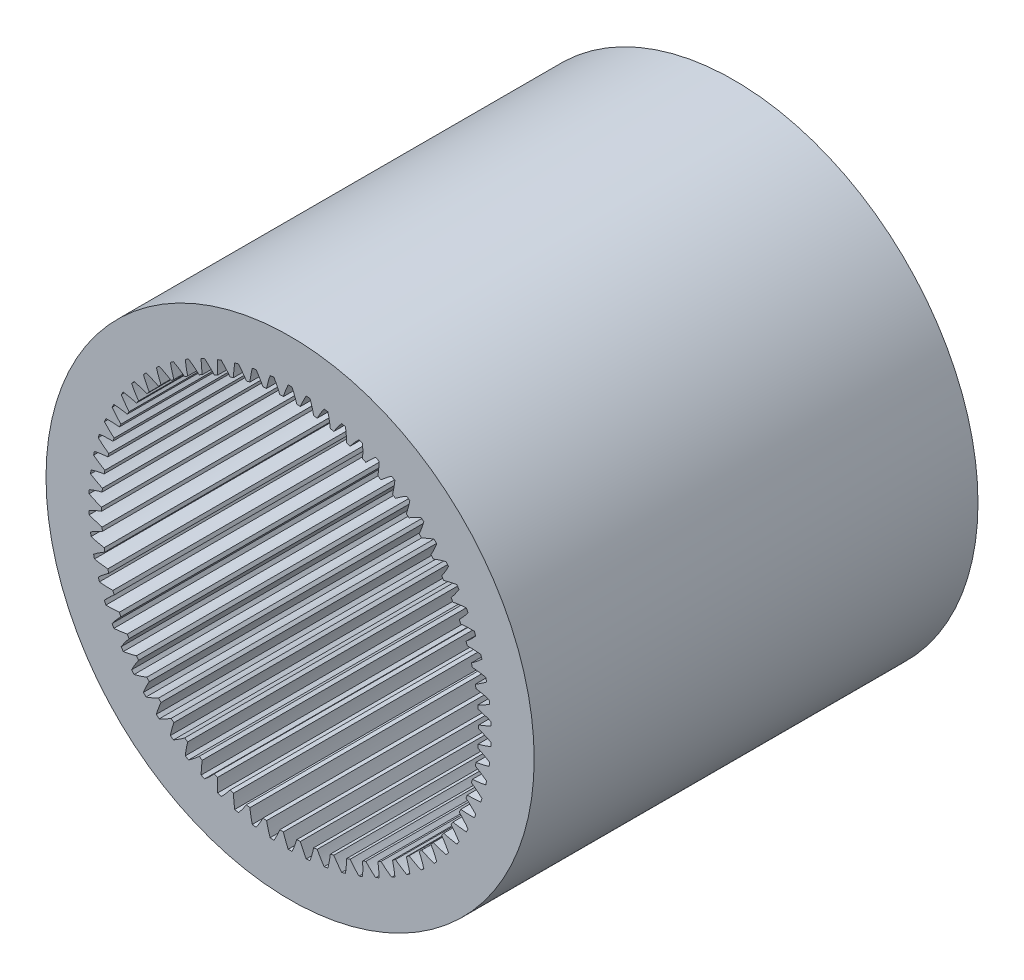
SolidWorks part; units mm, degrees
ref_plane "Front Plane" through (0, 0, 0) normal (0, 0, 1) x (1, 0, 0)
ref_plane "Top Plane" through (0, 0, 0) normal (0, 1, 0) x (1, 0, 0)
ref_plane "Right Plane" through (0, 0, 0) normal (1, 0, 0) x (0, 0, -1)
sketch "Sketch1" plane through (0, 0, 0) normal (0, 0, 1) x (1, 0, 0)
  circle A2 centre (0, 0) radius 11
  arc A4 (-8.3487, -1.5969) -> (-8.8549, -1.9333) centre (-6.1864, -5.4002) ccw
  arc A8 (-8.3774, -1.4384) -> (-8.3487, -1.5969) centre (0, 0) ccw
  arc A9 (-8.8549, -1.9333) -> (-8.8168, -2.1002) centre (0, 0) ccw
  arc A10 (-8.8168, -2.1002) -> (-8.2147, -2.1836) centre (-7.9168, 2.1812) ccw
  arc A11 (-8.4726, -0.6817) -> (-8.4582, -0.8421) centre (0, 0) ccw
  arc A12 (-8.4582, -0.8421) -> (-8.9926, -1.1317) centre (-6.6455, -4.8239) ccw
  arc A13 (-8.9926, -1.1317) -> (-8.9696, -1.3014) centre (0, 0) ccw
  arc A14 (-8.9696, -1.3014) -> (-8.3774, -1.4384) centre (-7.6894, 2.8821) ccw
  arc A15 (-8.4996, 0.0805) -> (-8.4996, -0.0805) centre (0, 0) ccw
  arc A16 (-8.4996, -0.0805) -> (-9.0578, -0.3211) centre (-7.0512, -4.2088) ccw
  arc A17 (-9.0578, -0.3211) -> (-9.0501, -0.4921) centre (0, 0) ccw
  arc A18 (-9.0501, -0.4921) -> (-8.4726, -0.6817) centre (-7.4001, 3.5598) ccw
  arc A19 (-8.4582, 0.8421) -> (-8.4726, 0.6817) centre (0, 0) ccw
  arc A20 (-8.4726, 0.6817) -> (-9.0501, 0.4921) centre (-7.4001, -3.5598) ccw
  arc A21 (-9.0501, 0.4921) -> (-9.0578, 0.3211) centre (0, 0) ccw
  arc A22 (-9.0578, 0.3211) -> (-8.4996, 0.0805) centre (-7.0512, 4.2088) ccw
  arc A23 (-8.3487, 1.5969) -> (-8.3774, 1.4384) centre (0, 0) ccw
  arc A24 (-8.3774, 1.4384) -> (-8.9696, 1.3014) centre (-7.6894, -2.8821) ccw
  arc A25 (-8.9696, 1.3014) -> (-8.9926, 1.1317) centre (0, 0) ccw
  arc A26 (-8.9926, 1.1317) -> (-8.4582, 0.8421) centre (-6.6455, 4.8239) ccw
  arc A27 (-8.1719, 2.3388) -> (-8.2147, 2.1836) centre (0, 0) ccw
  arc A28 (-8.2147, 2.1836) -> (-8.8168, 2.1002) centre (-7.9168, -2.1812) ccw
  arc A29 (-8.8168, 2.1002) -> (-8.8549, 1.9333) centre (0, 0) ccw
  arc A30 (-8.8549, 1.9333) -> (-8.3487, 1.5969) centre (-6.1864, 5.4002) ccw
  arc A31 (-7.9294, 3.0619) -> (-7.9859, 2.9112) centre (0, 0) ccw
  arc A32 (-7.9859, 2.9112) -> (-8.5931, 2.8821) centre (-8.0804, -1.4628) ccw
  arc A33 (-8.5931, 2.8821) -> (-8.646, 2.7192) centre (0, 0) ccw
  arc A34 (-8.646, 2.7192) -> (-8.1719, 2.3388) centre (-5.6774, 5.933) ccw
  arc A35 (-7.623, 3.7604) -> (-7.6928, 3.6153) centre (0, 0) ccw
  arc A36 (-7.6928, 3.6153) -> (-8.3001, 3.6407) centre (-8.179, -0.7326) ccw
  arc A37 (-8.3001, 3.6407) -> (-8.3674, 3.4833) centre (0, 0) ccw
  arc A38 (-8.3674, 3.4833) -> (-7.9294, 3.0619) centre (-5.1227, 6.418) ccw
  arc A39 (-7.2552, 4.4286) -> (-7.3378, 4.2903) centre (0, 0) ccw
  arc A40 (-7.3378, 4.2903) -> (-7.9404, 4.3701) centre (-8.2118, 0.0035) ccw
  arc A41 (-7.9404, 4.3701) -> (-8.0215, 4.2193) centre (0, 0) ccw
  arc A42 (-8.0215, 4.2193) -> (-7.623, 3.7604) centre (-4.5268, 6.8514) ccw
  arc A43 (-6.829, 5.0611) -> (-6.9237, 4.9308) centre (0, 0) ccw
  arc A44 (-6.9237, 4.9308) -> (-7.5167, 5.0643) centre (-8.1784, 0.7396) ccw
  arc A45 (-7.5167, 5.0643) -> (-7.611, 4.9214) centre (0, 0) ccw
  arc A46 (-7.611, 4.9214) -> (-7.2552, 4.4286) centre (-3.8944, 7.2296) ccw
  arc A47 (-6.3478, 5.6529) -> (-6.4538, 5.5316) centre (0, 0) ccw
  arc A48 (-6.4538, 5.5316) -> (-7.0324, 5.7177) centre (-8.0792, 1.4697) ccw
  arc A49 (-7.0324, 5.7177) -> (-7.1392, 5.5838) centre (0, 0) ccw
  arc A50 (-7.1392, 5.5838) -> (-6.829, 5.0611) centre (-3.2307, 7.5496) ccw
  arc A51 (-5.8156, 6.1991) -> (-5.932, 6.0878) centre (0, 0) ccw
  arc A52 (-5.932, 6.0878) -> (-6.4916, 6.325) centre (-7.9149, 2.188) ccw
  arc A53 (-6.4916, 6.325) -> (-6.6099, 6.2013) centre (0, 0) ccw
  arc A54 (-6.6099, 6.2013) -> (-6.3478, 5.6529) centre (-2.5409, 7.8088) ccw
  arc A55 (-5.2365, 6.6955) -> (-5.3624, 6.5951) centre (0, 0) ccw
  arc A56 (-5.3624, 6.5951) -> (-5.8985, 6.8815) centre (-7.6869, 2.8887) ccw
  arc A57 (-5.8985, 6.8815) -> (-6.0274, 6.7688) centre (0, 0) ccw
  arc A58 (-6.0274, 6.7688) -> (-5.8156, 6.1991) centre (-1.8307, 8.0051) ccw
  arc A59 (-4.6152, 7.1379) -> (-4.7496, 7.0492) centre (0, 0) ccw
  arc A60 (-4.7496, 7.0492) -> (-5.2579, 7.3825) centre (-7.397, 3.5661) ccw
  arc A61 (-5.2579, 7.3825) -> (-5.3964, 7.2819) centre (0, 0) ccw
  arc A62 (-5.3964, 7.2819) -> (-5.2365, 6.6955) centre (-1.1058, 8.137) ccw
  arc A63 (-3.9568, 7.5229) -> (-4.0986, 7.4466) centre (0, 0) ccw
  arc A64 (-4.0986, 7.4466) -> (-4.575, 7.8241) centre (-7.0476, 4.2148) ccw
  arc A65 (-4.575, 7.8241) -> (-4.7219, 7.7363) centre (0, 0) ccw
  arc A66 (-4.7219, 7.7363) -> (-4.6152, 7.1379) centre (-0.3719, 8.2033) ccw
  arc A67 (-3.2665, 7.8473) -> (-3.4146, 7.784) centre (0, 0) ccw
  arc A68 (-3.4146, 7.784) -> (-3.8552, 8.2027) centre (-6.6414, 4.8296) ccw
  arc A69 (-3.8552, 8.2027) -> (-4.0095, 8.1284) centre (0, 0) ccw
  arc A70 (-4.0095, 8.1284) -> (-3.9568, 7.5229) centre (0.3649, 8.2037) ccw
  arc A71 (-2.55, 8.1085) -> (-2.7031, 8.0587) centre (0, 0) ccw
  arc A72 (-2.7031, 8.0587) -> (-3.1044, 8.5153) centre (-6.1817, 5.4055) ccw
  arc A73 (-3.1044, 8.5153) -> (-3.2647, 8.4551) centre (0, 0) ccw
  arc A74 (-3.2647, 8.4551) -> (-3.2665, 7.8473) centre (1.0988, 8.1379) ccw
  arc A75 (-1.8129, 8.3044) -> (-1.9698, 8.2686) centre (0, 0) ccw
  arc A76 (-1.9698, 8.2686) -> (-2.3286, 8.7593) centre (-5.6723, 5.9379) ccw
  arc A77 (-2.3286, 8.7593) -> (-2.4936, 8.7137) centre (0, 0) ccw
  arc A78 (-2.4936, 8.7137) -> (-2.55, 8.1085) centre (1.8239, 8.0067) ccw
  arc A79 (-1.0611, 8.4335) -> (-1.2207, 8.4119) centre (0, 0) ccw
  arc A80 (-1.2207, 8.4119) -> (-1.5341, 8.9327) centre (-5.1172, 6.4224) ccw
  arc A81 (-1.5341, 8.9327) -> (-1.7025, 8.9022) centre (0, 0) ccw
  arc A82 (-1.7025, 8.9022) -> (-1.8129, 8.3044) centre (2.5342, 7.8109) ccw
  arc A83 (-0.3009, 8.4947) -> (-0.4618, 8.4874) centre (0, 0) ccw
  arc A84 (-0.4618, 8.4874) -> (-0.7272, 9.0343) centre (-4.5209, 6.8553) ccw
  arc A85 (-0.7272, 9.0343) -> (-0.8977, 9.0189) centre (0, 0) ccw
  arc A86 (-0.8977, 9.0189) -> (-1.0611, 8.4335) centre (3.2242, 7.5523) ccw
  arc A87 (0.4618, 8.4874) -> (0.3009, 8.4947) centre (0, 0) ccw
  arc A88 (0.3009, 8.4947) -> (0.0856, 9.0631) centre (-3.8882, 7.2329) ccw
  arc A89 (0.0856, 9.0631) -> (-0.0856, 9.0631) centre (0, 0) ccw
  arc A90 (-0.0856, 9.0631) -> (-0.3009, 8.4947) centre (3.8882, 7.2329) ccw
  arc A91 (1.2207, 8.4119) -> (1.0611, 8.4335) centre (0, 0) ccw
  arc A92 (1.0611, 8.4335) -> (0.8977, 9.0189) centre (-3.2242, 7.5523) ccw
  arc A93 (0.8977, 9.0189) -> (0.7272, 9.0343) centre (0, 0) ccw
  arc A94 (0.7272, 9.0343) -> (0.4618, 8.4874) centre (4.5209, 6.8553) ccw
  arc A95 (1.9698, 8.2686) -> (1.8129, 8.3044) centre (0, 0) ccw
  arc A96 (1.8129, 8.3044) -> (1.7025, 8.9022) centre (-2.5342, 7.8109) ccw
  arc A97 (1.7025, 8.9022) -> (1.5341, 8.9327) centre (0, 0) ccw
  arc A98 (1.5341, 8.9327) -> (1.2207, 8.4119) centre (5.1172, 6.4224) ccw
  arc A99 (2.7031, 8.0587) -> (2.55, 8.1085) centre (0, 0) ccw
  arc A100 (2.55, 8.1085) -> (2.4936, 8.7137) centre (-1.8239, 8.0067) ccw
  arc A101 (2.4936, 8.7137) -> (2.3286, 8.7593) centre (0, 0) ccw
  arc A102 (2.3286, 8.7593) -> (1.9698, 8.2686) centre (5.6723, 5.9379) ccw
  arc A103 (3.4146, 7.784) -> (3.2665, 7.8473) centre (0, 0) ccw
  arc A104 (3.2665, 7.8473) -> (3.2647, 8.4551) centre (-1.0988, 8.1379) ccw
  arc A105 (3.2647, 8.4551) -> (3.1044, 8.5153) centre (0, 0) ccw
  arc A106 (3.1044, 8.5153) -> (2.7031, 8.0587) centre (6.1817, 5.4055) ccw
  arc A107 (4.0986, 7.4466) -> (3.9568, 7.5229) centre (0, 0) ccw
  arc A108 (3.9568, 7.5229) -> (4.0095, 8.1284) centre (-0.3649, 8.2037) ccw
  arc A109 (4.0095, 8.1284) -> (3.8552, 8.2027) centre (0, 0) ccw
  arc A110 (3.8552, 8.2027) -> (3.4146, 7.784) centre (6.6414, 4.8296) ccw
  arc A111 (4.7496, 7.0492) -> (4.6152, 7.1379) centre (0, 0) ccw
  arc A112 (4.6152, 7.1379) -> (4.7219, 7.7363) centre (0.3719, 8.2033) ccw
  arc A113 (4.7219, 7.7363) -> (4.575, 7.8241) centre (0, 0) ccw
  arc A114 (4.575, 7.8241) -> (4.0986, 7.4466) centre (7.0476, 4.2148) ccw
  arc A115 (5.3624, 6.5951) -> (5.2365, 6.6955) centre (0, 0) ccw
  arc A116 (5.2365, 6.6955) -> (5.3964, 7.2819) centre (1.1058, 8.137) ccw
  arc A117 (5.3964, 7.2819) -> (5.2579, 7.3825) centre (0, 0) ccw
  arc A118 (5.2579, 7.3825) -> (4.7496, 7.0492) centre (7.397, 3.5661) ccw
  arc A119 (5.932, 6.0878) -> (5.8156, 6.1991) centre (0, 0) ccw
  arc A120 (5.8156, 6.1991) -> (6.0274, 6.7688) centre (1.8307, 8.0051) ccw
  arc A121 (6.0274, 6.7688) -> (5.8985, 6.8815) centre (0, 0) ccw
  arc A122 (5.8985, 6.8815) -> (5.3624, 6.5951) centre (7.6869, 2.8887) ccw
  arc A123 (6.4538, 5.5316) -> (6.3478, 5.6529) centre (0, 0) ccw
  arc A124 (6.3478, 5.6529) -> (6.6099, 6.2013) centre (2.5409, 7.8088) ccw
  arc A125 (6.6099, 6.2013) -> (6.4916, 6.325) centre (0, 0) ccw
  arc A126 (6.4916, 6.325) -> (5.932, 6.0878) centre (7.9149, 2.188) ccw
  arc A127 (6.9237, 4.9308) -> (6.829, 5.0611) centre (0, 0) ccw
  arc A128 (6.829, 5.0611) -> (7.1392, 5.5838) centre (3.2307, 7.5496) ccw
  arc A129 (7.1392, 5.5838) -> (7.0324, 5.7177) centre (0, 0) ccw
  arc A130 (7.0324, 5.7177) -> (6.4538, 5.5316) centre (8.0792, 1.4697) ccw
  arc A131 (7.3378, 4.2903) -> (7.2552, 4.4286) centre (0, 0) ccw
  arc A132 (7.2552, 4.4286) -> (7.611, 4.9214) centre (3.8944, 7.2296) ccw
  arc A133 (7.611, 4.9214) -> (7.5167, 5.0643) centre (0, 0) ccw
  arc A134 (7.5167, 5.0643) -> (6.9237, 4.9308) centre (8.1784, 0.7396) ccw
  arc A135 (7.6928, 3.6153) -> (7.623, 3.7604) centre (0, 0) ccw
  arc A136 (7.623, 3.7604) -> (8.0215, 4.2193) centre (4.5268, 6.8514) ccw
  arc A137 (8.0215, 4.2193) -> (7.9404, 4.3701) centre (0, 0) ccw
  arc A138 (7.9404, 4.3701) -> (7.3378, 4.2903) centre (8.2118, 0.0035) ccw
  arc A139 (7.9859, 2.9112) -> (7.9294, 3.0619) centre (0, 0) ccw
  arc A140 (7.9294, 3.0619) -> (8.3674, 3.4833) centre (5.1227, 6.418) ccw
  arc A141 (8.3674, 3.4833) -> (8.3001, 3.6407) centre (0, 0) ccw
  arc A142 (8.3001, 3.6407) -> (7.6928, 3.6153) centre (8.179, -0.7326) ccw
  arc A143 (8.2147, 2.1836) -> (8.1719, 2.3388) centre (0, 0) ccw
  arc A144 (8.1719, 2.3388) -> (8.646, 2.7192) centre (5.6774, 5.933) ccw
  arc A145 (8.646, 2.7192) -> (8.5931, 2.8821) centre (0, 0) ccw
  arc A146 (8.5931, 2.8821) -> (7.9859, 2.9112) centre (8.0804, -1.4628) ccw
  arc A147 (8.3774, 1.4384) -> (8.3487, 1.5969) centre (0, 0) ccw
  arc A148 (8.3487, 1.5969) -> (8.8549, 1.9333) centre (6.1864, 5.4002) ccw
  arc A149 (8.8549, 1.9333) -> (8.8168, 2.1002) centre (0, 0) ccw
  arc A150 (8.8168, 2.1002) -> (8.2147, 2.1836) centre (7.9168, -2.1812) ccw
  arc A151 (8.4726, 0.6817) -> (8.4582, 0.8421) centre (0, 0) ccw
  arc A152 (8.4582, 0.8421) -> (8.9926, 1.1317) centre (6.6455, 4.8239) ccw
  arc A153 (8.9926, 1.1317) -> (8.9696, 1.3014) centre (0, 0) ccw
  arc A154 (8.9696, 1.3014) -> (8.3774, 1.4384) centre (7.6894, -2.8821) ccw
  arc A155 (8.4996, -0.0805) -> (8.4996, 0.0805) centre (0, 0) ccw
  arc A156 (8.4996, 0.0805) -> (9.0578, 0.3211) centre (7.0512, 4.2088) ccw
  arc A157 (9.0578, 0.3211) -> (9.0501, 0.4921) centre (0, 0) ccw
  arc A158 (9.0501, 0.4921) -> (8.4726, 0.6817) centre (7.4001, -3.5598) ccw
  arc A159 (8.4582, -0.8421) -> (8.4726, -0.6817) centre (0, 0) ccw
  arc A160 (8.4726, -0.6817) -> (9.0501, -0.4921) centre (7.4001, 3.5598) ccw
  arc A161 (9.0501, -0.4921) -> (9.0578, -0.3211) centre (0, 0) ccw
  arc A162 (9.0578, -0.3211) -> (8.4996, -0.0805) centre (7.0512, -4.2088) ccw
  arc A163 (8.3487, -1.5969) -> (8.3774, -1.4384) centre (0, 0) ccw
  arc A164 (8.3774, -1.4384) -> (8.9696, -1.3014) centre (7.6894, 2.8821) ccw
  arc A165 (8.9696, -1.3014) -> (8.9926, -1.1317) centre (0, 0) ccw
  arc A166 (8.9926, -1.1317) -> (8.4582, -0.8421) centre (6.6455, -4.8239) ccw
  arc A167 (8.1719, -2.3388) -> (8.2147, -2.1836) centre (0, 0) ccw
  arc A168 (8.2147, -2.1836) -> (8.8168, -2.1002) centre (7.9168, 2.1812) ccw
  arc A169 (8.8168, -2.1002) -> (8.8549, -1.9333) centre (0, 0) ccw
  arc A170 (8.8549, -1.9333) -> (8.3487, -1.5969) centre (6.1864, -5.4002) ccw
  arc A171 (7.9294, -3.0619) -> (7.9859, -2.9112) centre (0, 0) ccw
  arc A172 (7.9859, -2.9112) -> (8.5931, -2.8821) centre (8.0804, 1.4628) ccw
  arc A173 (8.5931, -2.8821) -> (8.646, -2.7192) centre (0, 0) ccw
  arc A174 (8.646, -2.7192) -> (8.1719, -2.3388) centre (5.6774, -5.933) ccw
  arc A175 (7.623, -3.7604) -> (7.6928, -3.6153) centre (0, 0) ccw
  arc A176 (7.6928, -3.6153) -> (8.3001, -3.6407) centre (8.179, 0.7326) ccw
  arc A177 (8.3001, -3.6407) -> (8.3674, -3.4833) centre (0, 0) ccw
  arc A178 (8.3674, -3.4833) -> (7.9294, -3.0619) centre (5.1227, -6.418) ccw
  arc A179 (7.2552, -4.4286) -> (7.3378, -4.2903) centre (0, 0) ccw
  arc A180 (7.3378, -4.2903) -> (7.9404, -4.3701) centre (8.2118, -0.0035) ccw
  arc A181 (7.9404, -4.3701) -> (8.0215, -4.2193) centre (0, 0) ccw
  arc A182 (8.0215, -4.2193) -> (7.623, -3.7604) centre (4.5268, -6.8514) ccw
  arc A183 (6.829, -5.0611) -> (6.9237, -4.9308) centre (0, 0) ccw
  arc A184 (6.9237, -4.9308) -> (7.5167, -5.0643) centre (8.1784, -0.7396) ccw
  arc A185 (7.5167, -5.0643) -> (7.611, -4.9214) centre (0, 0) ccw
  arc A186 (7.611, -4.9214) -> (7.2552, -4.4286) centre (3.8944, -7.2296) ccw
  arc A187 (6.3478, -5.6529) -> (6.4538, -5.5316) centre (0, 0) ccw
  arc A188 (6.4538, -5.5316) -> (7.0324, -5.7177) centre (8.0792, -1.4697) ccw
  arc A189 (7.0324, -5.7177) -> (7.1392, -5.5838) centre (0, 0) ccw
  arc A190 (7.1392, -5.5838) -> (6.829, -5.0611) centre (3.2307, -7.5496) ccw
  arc A191 (5.8156, -6.1991) -> (5.932, -6.0878) centre (0, 0) ccw
  arc A192 (5.932, -6.0878) -> (6.4916, -6.325) centre (7.9149, -2.188) ccw
  arc A193 (6.4916, -6.325) -> (6.6099, -6.2013) centre (0, 0) ccw
  arc A194 (6.6099, -6.2013) -> (6.3478, -5.6529) centre (2.5409, -7.8088) ccw
  arc A195 (5.2365, -6.6955) -> (5.3624, -6.5951) centre (0, 0) ccw
  arc A196 (5.3624, -6.5951) -> (5.8985, -6.8815) centre (7.6869, -2.8887) ccw
  arc A197 (5.8985, -6.8815) -> (6.0274, -6.7688) centre (0, 0) ccw
  arc A198 (6.0274, -6.7688) -> (5.8156, -6.1991) centre (1.8307, -8.0051) ccw
  arc A199 (4.6152, -7.1379) -> (4.7496, -7.0492) centre (0, 0) ccw
  arc A200 (4.7496, -7.0492) -> (5.2579, -7.3825) centre (7.397, -3.5661) ccw
  arc A201 (5.2579, -7.3825) -> (5.3964, -7.2819) centre (0, 0) ccw
  arc A202 (5.3964, -7.2819) -> (5.2365, -6.6955) centre (1.1058, -8.137) ccw
  arc A203 (3.9568, -7.5229) -> (4.0986, -7.4466) centre (0, 0) ccw
  arc A204 (4.0986, -7.4466) -> (4.575, -7.8241) centre (7.0476, -4.2148) ccw
  arc A205 (4.575, -7.8241) -> (4.7219, -7.7363) centre (0, 0) ccw
  arc A206 (4.7219, -7.7363) -> (4.6152, -7.1379) centre (0.3719, -8.2033) ccw
  arc A207 (3.2665, -7.8473) -> (3.4146, -7.784) centre (0, 0) ccw
  arc A208 (3.4146, -7.784) -> (3.8552, -8.2027) centre (6.6414, -4.8296) ccw
  arc A209 (3.8552, -8.2027) -> (4.0095, -8.1284) centre (0, 0) ccw
  arc A210 (4.0095, -8.1284) -> (3.9568, -7.5229) centre (-0.3649, -8.2037) ccw
  arc A211 (2.55, -8.1085) -> (2.7031, -8.0587) centre (0, 0) ccw
  arc A212 (2.7031, -8.0587) -> (3.1044, -8.5153) centre (6.1817, -5.4055) ccw
  arc A213 (3.1044, -8.5153) -> (3.2647, -8.4551) centre (0, 0) ccw
  arc A214 (3.2647, -8.4551) -> (3.2665, -7.8473) centre (-1.0988, -8.1379) ccw
  arc A215 (1.8129, -8.3044) -> (1.9698, -8.2686) centre (0, 0) ccw
  arc A216 (1.9698, -8.2686) -> (2.3286, -8.7593) centre (5.6723, -5.9379) ccw
  arc A217 (2.3286, -8.7593) -> (2.4936, -8.7137) centre (0, 0) ccw
  arc A218 (2.4936, -8.7137) -> (2.55, -8.1085) centre (-1.8239, -8.0067) ccw
  arc A219 (1.0611, -8.4335) -> (1.2207, -8.4119) centre (0, 0) ccw
  arc A220 (1.2207, -8.4119) -> (1.5341, -8.9327) centre (5.1172, -6.4224) ccw
  arc A221 (1.5341, -8.9327) -> (1.7025, -8.9022) centre (0, 0) ccw
  arc A222 (1.7025, -8.9022) -> (1.8129, -8.3044) centre (-2.5342, -7.8109) ccw
  arc A223 (0.3009, -8.4947) -> (0.4618, -8.4874) centre (0, 0) ccw
  arc A224 (0.4618, -8.4874) -> (0.7272, -9.0343) centre (4.5209, -6.8553) ccw
  arc A225 (0.7272, -9.0343) -> (0.8977, -9.0189) centre (0, 0) ccw
  arc A226 (0.8977, -9.0189) -> (1.0611, -8.4335) centre (-3.2242, -7.5523) ccw
  arc A227 (-0.4618, -8.4874) -> (-0.3009, -8.4947) centre (0, 0) ccw
  arc A228 (-0.3009, -8.4947) -> (-0.0856, -9.0631) centre (3.8882, -7.2329) ccw
  arc A229 (-0.0856, -9.0631) -> (0.0856, -9.0631) centre (0, 0) ccw
  arc A230 (0.0856, -9.0631) -> (0.3009, -8.4947) centre (-3.8882, -7.2329) ccw
  arc A231 (-1.2207, -8.4119) -> (-1.0611, -8.4335) centre (0, 0) ccw
  arc A232 (-1.0611, -8.4335) -> (-0.8977, -9.0189) centre (3.2242, -7.5523) ccw
  arc A233 (-0.8977, -9.0189) -> (-0.7272, -9.0343) centre (0, 0) ccw
  arc A234 (-0.7272, -9.0343) -> (-0.4618, -8.4874) centre (-4.5209, -6.8553) ccw
  arc A235 (-1.9698, -8.2686) -> (-1.8129, -8.3044) centre (0, 0) ccw
  arc A236 (-1.8129, -8.3044) -> (-1.7025, -8.9022) centre (2.5342, -7.8109) ccw
  arc A237 (-1.7025, -8.9022) -> (-1.5341, -8.9327) centre (0, 0) ccw
  arc A238 (-1.5341, -8.9327) -> (-1.2207, -8.4119) centre (-5.1172, -6.4224) ccw
  arc A239 (-2.7031, -8.0587) -> (-2.55, -8.1085) centre (0, 0) ccw
  arc A240 (-2.55, -8.1085) -> (-2.4936, -8.7137) centre (1.8239, -8.0067) ccw
  arc A241 (-2.4936, -8.7137) -> (-2.3286, -8.7593) centre (0, 0) ccw
  arc A242 (-2.3286, -8.7593) -> (-1.9698, -8.2686) centre (-5.6723, -5.9379) ccw
  arc A243 (-3.4146, -7.784) -> (-3.2665, -7.8473) centre (0, 0) ccw
  arc A244 (-3.2665, -7.8473) -> (-3.2647, -8.4551) centre (1.0988, -8.1379) ccw
  arc A245 (-3.2647, -8.4551) -> (-3.1044, -8.5153) centre (0, 0) ccw
  arc A246 (-3.1044, -8.5153) -> (-2.7031, -8.0587) centre (-6.1817, -5.4055) ccw
  arc A247 (-4.0986, -7.4466) -> (-3.9568, -7.5229) centre (0, 0) ccw
  arc A248 (-3.9568, -7.5229) -> (-4.0095, -8.1284) centre (0.3649, -8.2037) ccw
  arc A249 (-4.0095, -8.1284) -> (-3.8552, -8.2027) centre (0, 0) ccw
  arc A250 (-3.8552, -8.2027) -> (-3.4146, -7.784) centre (-6.6414, -4.8296) ccw
  arc A251 (-4.7496, -7.0492) -> (-4.6152, -7.1379) centre (0, 0) ccw
  arc A252 (-4.6152, -7.1379) -> (-4.7219, -7.7363) centre (-0.3719, -8.2033) ccw
  arc A253 (-4.7219, -7.7363) -> (-4.575, -7.8241) centre (0, 0) ccw
  arc A254 (-4.575, -7.8241) -> (-4.0986, -7.4466) centre (-7.0476, -4.2148) ccw
  arc A255 (-5.3624, -6.5951) -> (-5.2365, -6.6955) centre (0, 0) ccw
  arc A256 (-5.2365, -6.6955) -> (-5.3964, -7.2819) centre (-1.1058, -8.137) ccw
  arc A257 (-5.3964, -7.2819) -> (-5.2579, -7.3825) centre (0, 0) ccw
  arc A258 (-5.2579, -7.3825) -> (-4.7496, -7.0492) centre (-7.397, -3.5661) ccw
  arc A259 (-5.932, -6.0878) -> (-5.8156, -6.1991) centre (0, 0) ccw
  arc A260 (-5.8156, -6.1991) -> (-6.0274, -6.7688) centre (-1.8307, -8.0051) ccw
  arc A261 (-6.0274, -6.7688) -> (-5.8985, -6.8815) centre (0, 0) ccw
  arc A262 (-5.8985, -6.8815) -> (-5.3624, -6.5951) centre (-7.6869, -2.8887) ccw
  arc A263 (-6.4538, -5.5316) -> (-6.3478, -5.6529) centre (0, 0) ccw
  arc A264 (-6.3478, -5.6529) -> (-6.6099, -6.2013) centre (-2.5409, -7.8088) ccw
  arc A265 (-6.6099, -6.2013) -> (-6.4916, -6.325) centre (0, 0) ccw
  arc A266 (-6.4916, -6.325) -> (-5.932, -6.0878) centre (-7.9149, -2.188) ccw
  arc A267 (-6.9237, -4.9308) -> (-6.829, -5.0611) centre (0, 0) ccw
  arc A268 (-6.829, -5.0611) -> (-7.1392, -5.5838) centre (-3.2307, -7.5496) ccw
  arc A269 (-7.1392, -5.5838) -> (-7.0324, -5.7177) centre (0, 0) ccw
  arc A270 (-7.0324, -5.7177) -> (-6.4538, -5.5316) centre (-8.0792, -1.4697) ccw
  arc A271 (-7.3378, -4.2903) -> (-7.2552, -4.4286) centre (0, 0) ccw
  arc A272 (-7.2552, -4.4286) -> (-7.611, -4.9214) centre (-3.8944, -7.2296) ccw
  arc A273 (-7.611, -4.9214) -> (-7.5167, -5.0643) centre (0, 0) ccw
  arc A274 (-7.5167, -5.0643) -> (-6.9237, -4.9308) centre (-8.1784, -0.7396) ccw
  arc A275 (-7.6928, -3.6153) -> (-7.623, -3.7604) centre (0, 0) ccw
  arc A276 (-7.623, -3.7604) -> (-8.0215, -4.2193) centre (-4.5268, -6.8514) ccw
  arc A277 (-8.0215, -4.2193) -> (-7.9404, -4.3701) centre (0, 0) ccw
  arc A278 (-7.9404, -4.3701) -> (-7.3378, -4.2903) centre (-8.2118, -0.0035) ccw
  arc A279 (-7.9859, -2.9112) -> (-7.9294, -3.0619) centre (0, 0) ccw
  arc A280 (-7.9294, -3.0619) -> (-8.3674, -3.4833) centre (-5.1227, -6.418) ccw
  arc A281 (-8.3674, -3.4833) -> (-8.3001, -3.6407) centre (0, 0) ccw
  arc A282 (-8.3001, -3.6407) -> (-7.6928, -3.6153) centre (-8.179, 0.7326) ccw
  arc A283 (-8.2147, -2.1836) -> (-8.1719, -2.3388) centre (0, 0) ccw
  arc A284 (-8.1719, -2.3388) -> (-8.646, -2.7192) centre (-5.6774, -5.933) ccw
  arc A285 (-8.646, -2.7192) -> (-8.5931, -2.8821) centre (0, 0) ccw
  arc A286 (-8.5931, -2.8821) -> (-7.9859, -2.9112) centre (-8.0804, 1.4628) ccw
  dimension "D2" = 70
extrude "Boss-Extrude1" add sketch "Sketch1" along normal blind 20
ref_plane "Plane1" through (0, 0, 10) normal (0, 0, 1) x (1, 0, 0)
sketch "Sketch2" plane through (0, 0, 10) normal (0, 0, 1) x (1, 0, 0)
  line L0 (8.071, 9.5958) -> (1, 0)
  line L1 (1, 0) -> (5.8489, -11.0911)
  line L2 (4.2747, -11.7876) -> (-0.5, -0.866)
  line L3 (-0.5, -0.866) -> (-12.5296, 0.4803)
  line L4 (-12.3457, 2.1918) -> (-0.5, 0.866)
  line L5 (-0.5, 0.866) -> (6.6807, 10.6108)
  arc A0 (8.071, 9.5958) -> (5.8489, -11.0911) centre (0, 0) cw
  circle A1 centre (0, 0) radius 1
  arc A2 (4.2747, -11.7876) -> (-12.5296, 0.4803) centre (0, 0) cw
  arc A3 (-12.3457, 2.1918) -> (6.6807, 10.6108) centre (0, 0) cw
  dimension "D1" = 120
  dimension "D2" = 2
  dimension "D3" = 3
extrude "Cut-Extrude1" [suppressed] cut sketch "Sketch2" against normal mid plane 16 contours A2 L2 L3 | A3 L4 L5 | A0 L0 L1
move or copy body "Body-Move/Copy2" [suppressed] bodies to move or copy 102 copy no rotation origin (-0.326, 4.6142, 6.898) rotation axis (0.0585, -0.8285, 0.557) rotation angle 28.779
